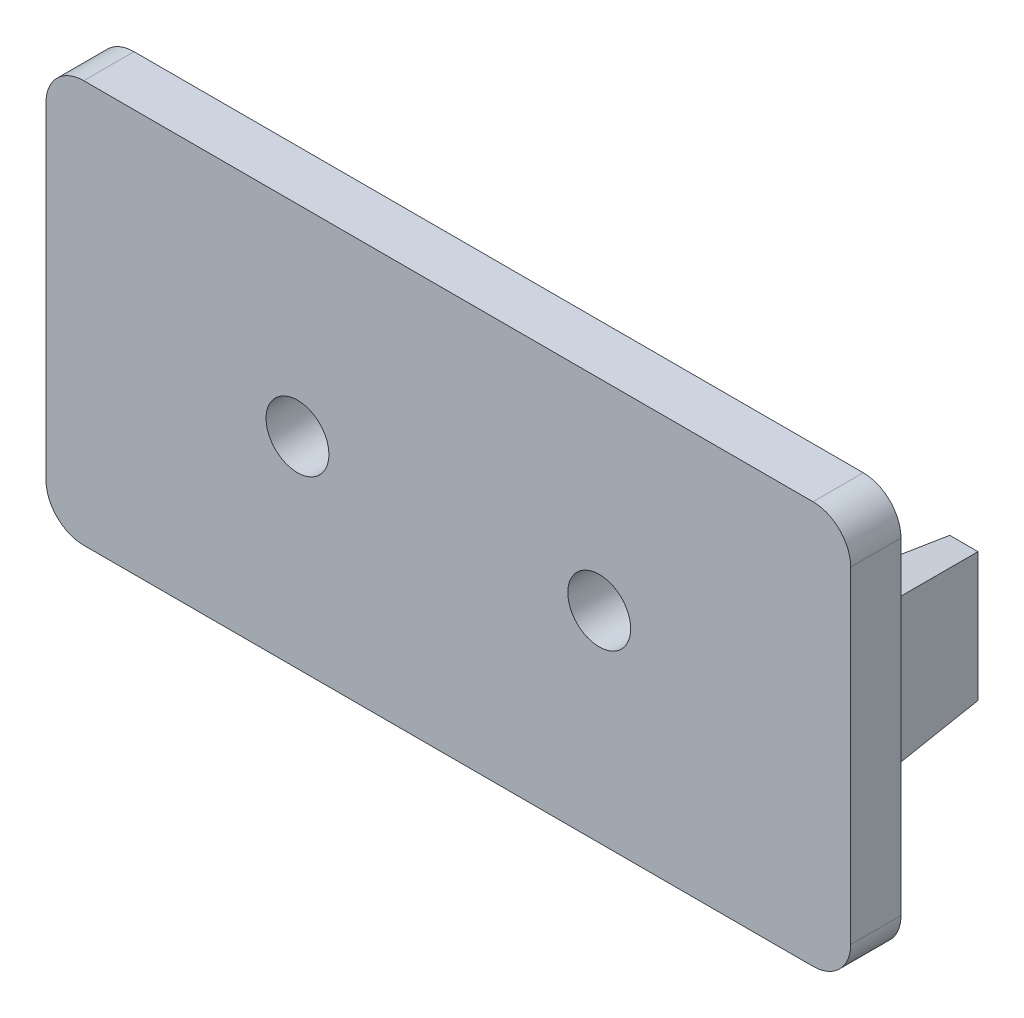
SolidWorks part; units mm, degrees
ref_plane "Front Plane" through (0, 0, 0) normal (0, 0, 1) x (1, 0, 0)
ref_plane "Top Plane" through (0, 0, 0) normal (0, 1, 0) x (1, 0, 0)
ref_plane "Right Plane" through (0, 0, 0) normal (1, 0, 0) x (0, 0, -1)
sketch "Sketch1" plane through (0, 0, 0) normal (0, 0, 1) x (1, 0, 0)
  line L1 (-16, 8) -> (16, 8)
  line L2 (-16, 8) -> (-16, -8)
  line L3 (-16, -8) -> (16, -8)
  line L4 (16, 8) -> (16, -8)
  circle A0 centre (6, 0) radius 1.25
  circle A1 centre (-6, 0) radius 1.25
  dimension "D5" = 2.5
  dimension "D6" = 2.5
  dimension "D1" = 16
  dimension "D2" = 8
  dimension "D3" = 32
  dimension "D4" = 16
  dimension "D7" = 6
  dimension "D8" = 6
extrude "Boss-Extrude1" add sketch "Sketch1" along normal blind 2
sketch "Sketch2" plane through (0, 0, 0) normal (0, 0, -1) x (-1, 0, 0)
  line L0 (-16, -8) -> (-16, 8) construction
  line L1 (-14.5, 3) -> (-12.5, 3)
  line L2 (-14.5, 3) -> (-14.5, -3)
  line L3 (-14.5, -3) -> (-12.5, -3)
  line L4 (-12.5, 3) -> (-12.5, -3)
  line L5 (12.5, 3) -> (14.5, 3)
  line L6 (12.5, 3) -> (12.5, -3)
  line L7 (12.5, -3) -> (14.5, -3)
  line L8 (14.5, 3) -> (14.5, -3)
  line L9 (-16, 8) -> (16, 8) construction
  line L10 (16, -8) -> (-16, -8) construction
  line L11 (16, 8) -> (16, -8) construction
  dimension "D1" = 2
  dimension "D2" = 1.5
  dimension "D3" = 5
  dimension "D4" = 5
  dimension "D5" = 5
  dimension "D6" = 1.5
  dimension "D7" = 2
  dimension "D8" = 5
extrude "Boss-Extrude2" add sketch "Sketch2" along normal blind 5 draft 5
fillet "Fillet1" radius 1.5 4 edges at (-16, -8, 1) (-16, 8, 1) (16, 8, 1) (16, -8, 1)
